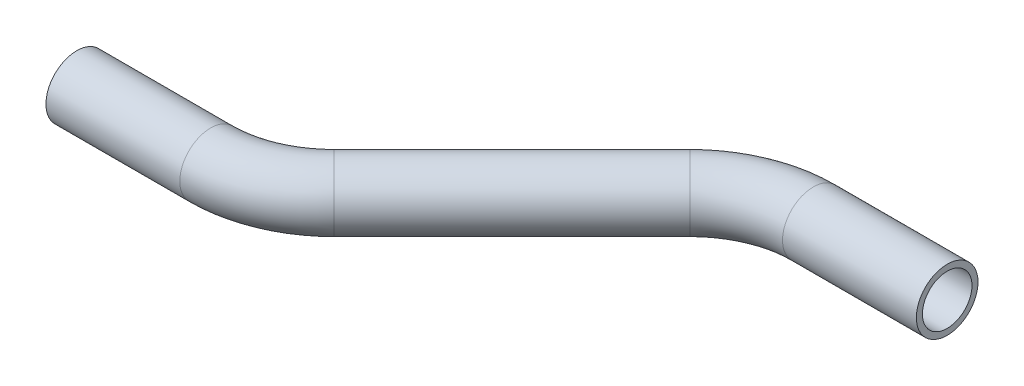
SolidWorks part; units mm, degrees
ref_plane "Front Plane" through (0, 0, 0) normal (0, 0, 1) x (1, 0, 0)
ref_plane "Top Plane" through (0, 0, 0) normal (0, 1, 0) x (1, 0, 0)
ref_plane "Right Plane" through (0, 0, 0) normal (1, 0, 0) x (0, 0, -1)
sketch "Sketch2" plane through (0, 0, 0) normal (0, 1, 0) x (1, 0, 0)
  line L0 (0, 0) -> (27.579, 0)
  line L1 (45.5395, 7.4395) -> (82.2225, 44.1225)
  line L2 (100.183, 51.562) -> (127.762, 51.562)
  arc A0 (82.2225, 44.1225) -> (100.183, 51.562) centre (100.183, 26.162) cw
  arc A1 (27.579, 0) -> (45.5395, 7.4395) centre (27.579, 25.4) ccw
  point P7 (89.662, 51.562)
  point P10 (38.1, 0)
  dimension "D5" = 25.4
  dimension "D1" = 38.1
  dimension "D2" = 38.1
  dimension "D3" = 51.562
  dimension "D4" = 135
ref_plane "Plane1" through (0, 0, 0) normal (1, 0, 0) x (0, 0, -1)
sketch "Sketch3" plane through (0, 0, 0) normal (1, 0, 0) x (0, 0, -1)
  circle A0 centre (0, 0) radius 6.35
  circle A1 centre (0, 0) radius 5.1054
  dimension "D1" = 12.7
  dimension "D2" = 1.2446
sweep "Sweep1" add profiles "Sketch3" path "Sketch2"
